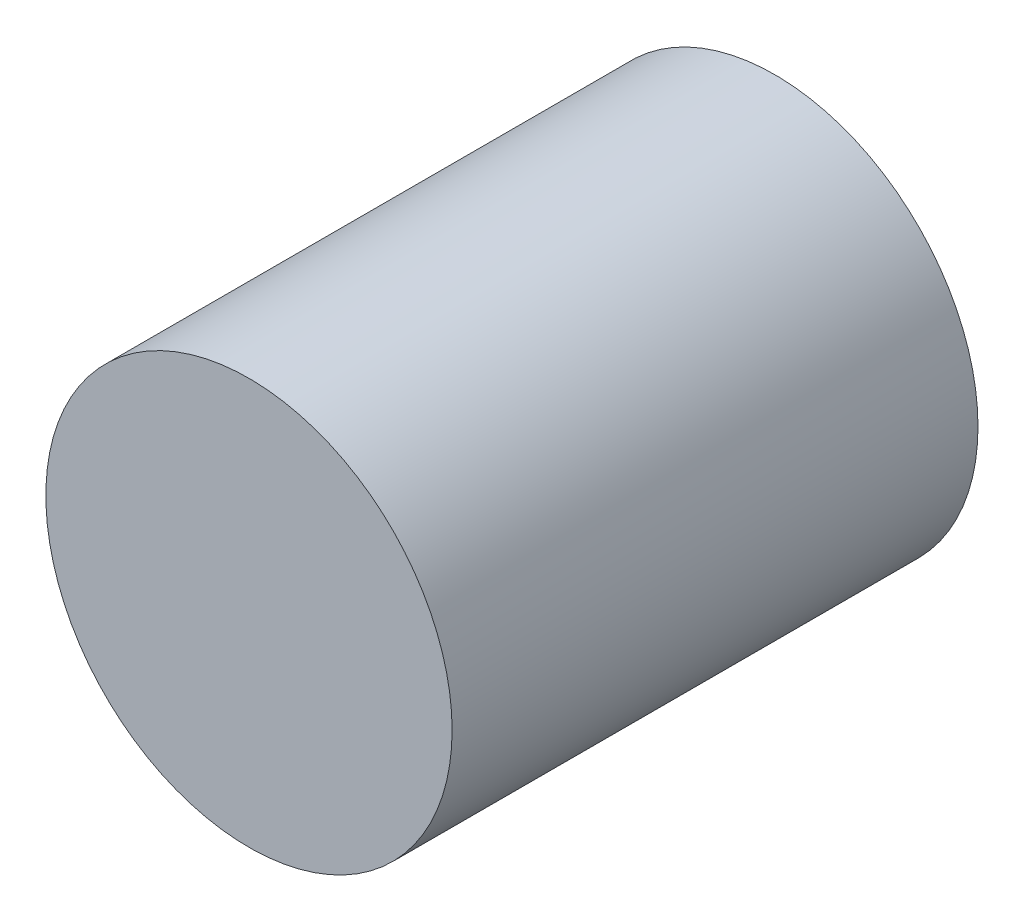
SolidWorks part; units mm, degrees
material "Brass"
ref_plane "Front Plane" through (0, 0, 0) normal (0, 0, 1) x (1, 0, 0)
ref_plane "Top Plane" through (0, 0, 0) normal (0, 1, 0) x (1, 0, 0)
ref_plane "Right Plane" through (0, 0, 0) normal (1, 0, 0) x (0, 0, -1)
sketch "Sketch1" plane through (0, 0, 0) normal (0, 0, 1) x (1, 0, 0)
  circle A0 centre (0, 0) radius 1.143
  dimension "D1" = 2.286
extrude "Boss-Extrude1" add sketch "Sketch1" along normal blind 2.9591
